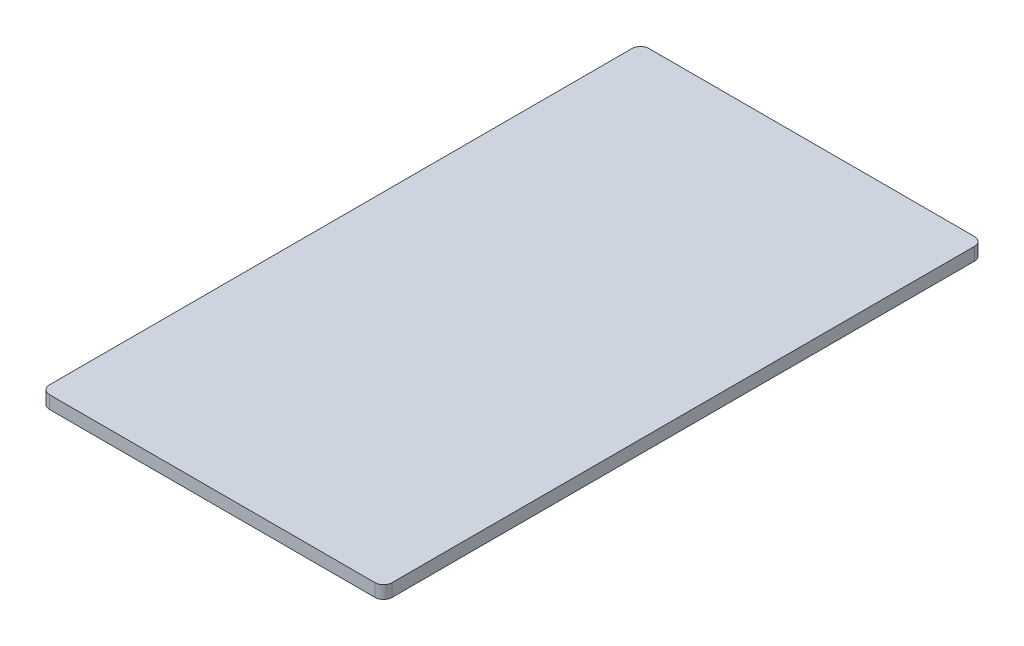
SolidWorks part; units mm, degrees
ref_plane "Спереди" through (0, 0, 0) normal (0, 0, 1) x (1, 0, 0)
ref_plane "Сверху" through (0, 0, 0) normal (0, 1, 0) x (1, 0, 0)
ref_plane "Справа" through (0, 0, 0) normal (1, 0, 0) x (0, 0, -1)
sketch "Эскиз1" plane through (0, 0, 0) normal (0, 1, 0) x (1, 0, 0)
  line L1 (-20, 35) -> (20, 35)
  line L2 (-20, 35) -> (-20, -35)
  line L3 (-20, -35) -> (20, -35)
  line L4 (20, 35) -> (20, -35)
  line L5 (-20, 35) -> (20, -35) construction
  line L6 (-20, -35) -> (20, 35) construction
  point P0 (0, 0)
  dimension "D1" = 70
  dimension "D2" = 40
extrude "Бобышка-Вытянуть1" add sketch "Эскиз1" along normal blind 1.5
sketch "Эскиз2" plane through (0, 1.5, 0) normal (0, 1, 0) x (1, 0, 0)
  line L0 (-20, -35) -> (20, -35) construction
  line L1 (10, -41) -> (-10, -41)
  line L2 (10, -41) -> (10, -35)
  line L3 (10, -35) -> (-10, -35)
  line L4 (-10, -41) -> (-10, -35)
  line L5 (10, -41) -> (-10, -35) construction
  line L6 (10, -35) -> (-10, -41) construction
  line L7 (20, 35) -> (-20, 35) construction
  line L8 (7.5, 41) -> (-7.5, 41)
  line L9 (7.5, 41) -> (7.5, 35)
  line L10 (7.5, 35) -> (-7.5, 35)
  line L11 (-7.5, 41) -> (-7.5, 35)
  line L12 (7.5, 41) -> (-7.5, 35) construction
  line L13 (7.5, 35) -> (-7.5, 41) construction
  point P0 (0, -38)
  point P9 (0, 38)
  dimension "D1" = 6
  dimension "D2" = 20
  dimension "D3" = 6
  dimension "D4" = 15
extrude "Бобышка-Вытянуть2" [suppressed] add sketch "Эскиз2" against normal blind 1.5
fillet "Скругление1" [suppressed] radius 1
fillet "Скругление2" radius 1 4 edges at (20, 0.75, -35) (-20, 0.75, -35) (20, 0.75, 35) (-20, 0.75, 35)
